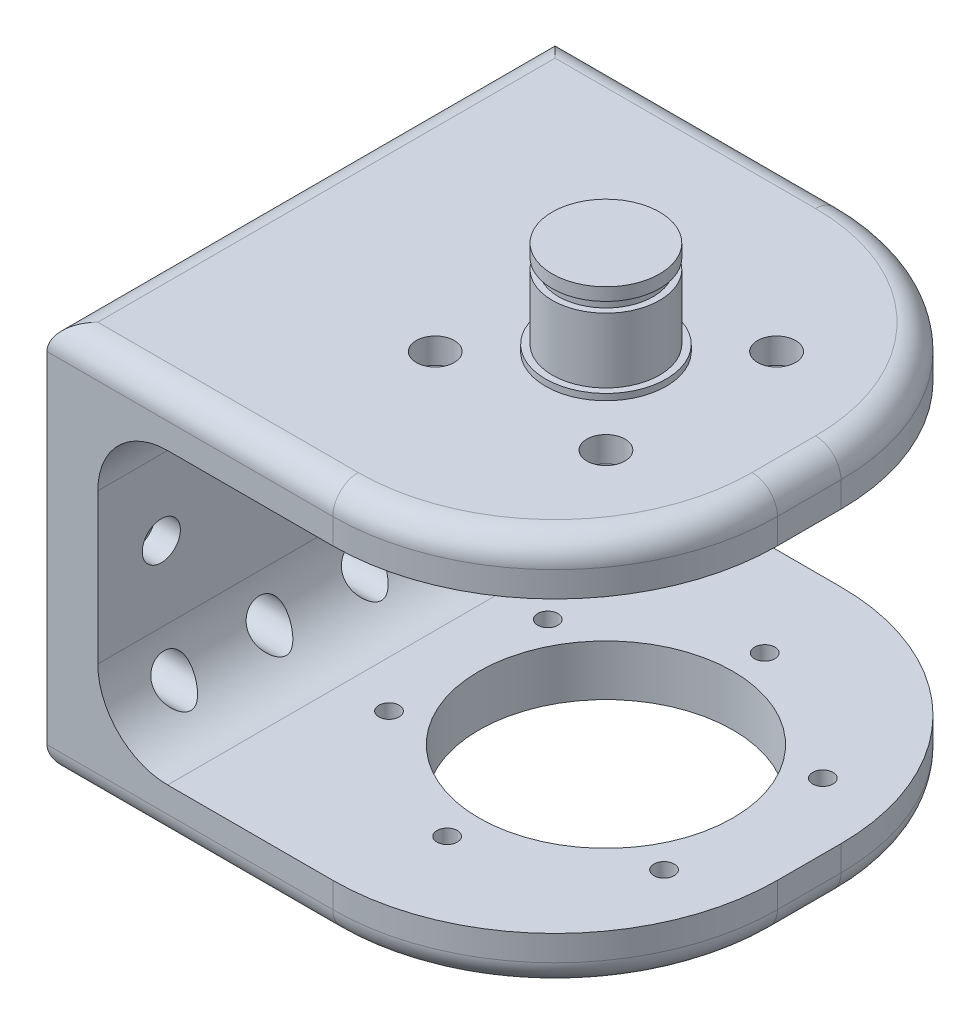
SolidWorks part; units mm, degrees
material "PETG-CF"
ref_plane "Front Plane" through (0, 0, 0) normal (0, 0, 1) x (1, 0, 0)
ref_plane "Top Plane" through (0, 0, 0) normal (0, 1, 0) x (1, 0, 0)
ref_plane "Right Plane" through (0, 0, 0) normal (1, 0, 0) x (0, 0, -1)
sketch "草图1" plane through (0, 0, 0) normal (0, 1, 0) x (1, 0, 0)
  line L1 (40, -40) -> (-40, -40)
  line L2 (40, -40) -> (40, 40)
  line L3 (40, 40) -> (-40, 40)
  line L4 (-40, -40) -> (-40, 40)
  line L5 (40, -40) -> (-40, 40) construction
  line L6 (40, 40) -> (-40, -40) construction
  point P0 (0, 0)
  dimension "D1" = 80
  dimension "D2" = 80
extrude "凸台-拉伸1" add sketch "草图1" along normal blind 8
sketch "草图2" plane through (0, 8, 0) normal (0, 1, 0) x (1, 0, 0)
  line L0 (-40, -40) -> (40, -40) construction
  line L1 (-32, -40) -> (-40, -40)
  line L2 (-32, -40) -> (-32, 40)
  line L3 (-32, 40) -> (-40, 40)
  line L4 (-40, -40) -> (-40, 40)
  line L5 (-32, -40) -> (-40, 40) construction
  line L6 (-32, 40) -> (-40, -40) construction
  point P0 (-36, 0)
  dimension "D1" = 8
extrude "凸台-拉伸2" add sketch "草图2" along normal blind 53.6
sketch "草图5" plane through (-32, 0, 0) normal (1, 0, 0) x (0, 0, -1)
  line L0 (-40, 61.6) -> (-40, 8) construction
  line L1 (40, 53.6) -> (-40, 53.6)
  line L2 (40, 53.6) -> (40, 61.6)
  line L3 (40, 61.6) -> (-40, 61.6)
  line L4 (-40, 53.6) -> (-40, 61.6)
  line L5 (40, 53.6) -> (-40, 61.6) construction
  line L6 (40, 61.6) -> (-40, 53.6) construction
  line L7 (40, 61.6) -> (40, 8) construction
  line L9 (-40, 61.6) -> (40, 61.6) construction
  point P0 (0, 57.6)
  dimension "D1" = 8
extrude "凸台-拉伸3" add sketch "草图5" along normal through all
sketch "草图4" plane through (0, 8, 0) normal (0, 1, 0) x (1, 0, 0)
  line L0 (-40, 40) -> (-40, -40) construction
  line L2 (40, -40) -> (40, 40) construction
  circle A0 centre (8, 0) radius 25 construction
  circle A1 centre (8, 25) radius 1.6
  circle A2 centre (-13.6506, 12.5) radius 1.6
  circle A3 centre (-13.6506, -12.5) radius 1.6
  circle A4 centre (8, -25) radius 1.6
  circle A5 centre (8, 0) radius 20
  circle A6 centre (29.6506, -12.5) radius 1.6
  circle A7 centre (29.6506, 12.5) radius 1.6
  point P17 (8, 0)
  point P22 (-40, 0)
  dimension "D3" = 50
  dimension "D4" = 3.2
  dimension "D6" = 40
  dimension "D1" = 32
  dimension "D5" = 6
extrude "切除-拉伸1" cut sketch "草图4" against normal through all contours A5 | A2 | A1 | A4 | A3 | A7 | A6
sketch "草图7" plane through (0, 61.6, 0) normal (0, 1, 0) x (1, 0, 0)
  line L0 (40, 40) -> (40, -40) construction
  line L3 (8, 0) -> (-5.435, 13.435) construction
  line L4 (8, 0) -> (8, 19) construction
  circle A0 centre (8, 0) radius 19 construction
  circle A5 centre (-5.435, 13.435) radius 1.6
  circle A6 centre (21.435, 13.435) radius 1.6
  circle A7 centre (21.435, -13.435) radius 1.6
  circle A8 centre (-5.435, -13.435) radius 1.6
  point P10 (40, 0)
  point P20 (8, 0)
  dimension "D1" = 38
  dimension "D4" = 45
  dimension "D5" = 3.2
  dimension "D6" = 4
extrude "切除-拉伸3" cut sketch "草图7" against normal up to next
fillet "圆角3" radius 35 4 edges at (40, 4, 40) (40, 4, -40) (40, 57.6, -40) (40, 57.6, 40)
fillet "圆角4" radius 11 2 edges at (-32, 8, 0) (-32, 53.6, 0)
sketch "草图6" plane through (-40, 0, 0) normal (-1, 0, 0) x (0, 0, 1)
  line L1 (30, 13) -> (-30, 13) construction
  line L2 (30, 13) -> (30, 48.6) construction
  line L3 (30, 48.6) -> (-30, 48.6) construction
  line L4 (-30, 13) -> (-30, 48.6) construction
  line L5 (30, 13) -> (-30, 48.6) construction
  line L6 (30, 48.6) -> (-30, 13) construction
  line L8 (40, 61.6) -> (40, 0) construction
  line L9 (-40, 61.6) -> (-40, 0) construction
  line L10 (-30, 30.8) -> (30, 30.8) construction
  line L11 (0, 13) -> (0, 48.6) construction
  line L12 (-40, 61.6) -> (40, 61.6) construction
  line L13 (-40, 0) -> (40, 0) construction
  circle A0 centre (-30, 48.6) radius 1.6
  circle A1 centre (30, 48.6) radius 1.6
  circle A2 centre (30, 13) radius 1.6
  circle A3 centre (-30, 13) radius 1.6
  circle A4 centre (-15, 13) radius 1.6
  circle A5 centre (0, 13) radius 1.6
  circle A6 centre (15, 13) radius 1.6
  circle A7 centre (-30, 30.8) radius 1.6
  circle A8 centre (30, 30.8) radius 1.6
  point P0 (0, 30.8)
  dimension "D5" = 3.2
  dimension "D1" = 13
  dimension "D2" = 13
  dimension "D3" = 10
  dimension "D4" = 10
  dimension "D6" = 4
  dimension "D7" = 2
extrude "切除-拉伸2" cut sketch "草图6" against normal through all
sketch "草图8" plane through (0, 61.6, 0) normal (0, 1, 0) x (1, 0, 0)
  circle A0 centre (8, 0) radius 8.45
  dimension "D1" = 16.9
extrude "凸台-拉伸4" add sketch "草图8" along normal blind 14.8
ref_plane "基准面1" through (0, 74.4, 0) normal (0, 1, 0) x (1, 0, 0)
sketch "草图10" plane through (0, 74.4, 0) normal (0, 1, 0) x (1, 0, 0)
  circle A0 centre (8, 0) radius 8.45
  circle A1 centre (8, 0) radius 7.45
  dimension "D1" = 14.9
extrude "切除-拉伸4" cut sketch "草图10" against normal blind 1.6
ref_plane "基准面2" through (-36, 0, 0) normal (-1, 0, 0) x (0, 0, 1)
sketch "草图12" plane through (-36, 0, 0) normal (-1, 0, 0) x (0, 0, 1)
  line L0 (-40, 30.8) -> (40, 30.8) construction
  line L1 (-40, 61.6) -> (-40, 0) construction
  line L2 (40, 61.6) -> (40, 0) construction
  line L3 (0, 61.6) -> (0, 0) construction
  line L4 (8.45, 61.6) -> (-8.45, 61.6) construction
  line L5 (-30, 13) -> (-30, 30.8) construction
  circle A0 centre (-30, 48.6) radius 3
  circle A1 centre (30, 48.6) radius 3
  circle A2 centre (30, 13) radius 3
  circle A3 centre (-30, 13) radius 3
  circle A4 centre (-15, 13) radius 3
  circle A5 centre (0, 13) radius 3
  circle A6 centre (15, 13) radius 3
  circle A7 centre (-30, 30.8) radius 3
  circle A8 centre (30, 30.8) radius 3
  dimension "D1" = 6
  dimension "D4" = 17.8
  dimension "D2" = 4
  dimension "D3" = 2
extrude "切除-拉伸5" cut sketch "草图12" against normal up to next
sketch "草图14" plane through (0, 61.6, 0) normal (0, 1, 0) x (1, 0, 0)
  circle A0 centre (-5.435, 13.435) radius 3
  circle A1 centre (21.435, 13.435) radius 3
  circle A2 centre (21.435, -13.435) radius 3
  circle A3 centre (-5.435, -13.435) radius 3
  point P12 (8, 0)
  dimension "D1" = 6
  dimension "D2" = 4
extrude "切除-拉伸6" cut sketch "草图14" against normal blind 4
sketch "草图15" plane through (0, 0, 0) normal (0, -1, 0) x (1, 0, 0)
  circle A0 centre (-13.6506, 12.5) radius 3
  circle A1 centre (8, 25) radius 3
  circle A2 centre (29.6506, 12.5) radius 3
  circle A3 centre (29.6506, -12.5) radius 3
  circle A4 centre (8, -25) radius 3
  circle A5 centre (-13.6506, -12.5) radius 3
  point P15 (8, 0)
  dimension "D1" = 6
  dimension "D2" = 6
extrude "切除-拉伸7" cut sketch "草图15" against normal blind 4
sketch "草图16" plane through (0, 61.6, 0) normal (0, 1, 0) x (1, 0, 0)
  circle A0 centre (8, 0) radius 9.5
  dimension "D1" = 19
extrude "凸台-拉伸5" add sketch "草图16" along normal blind 1
fillet "Fillet2" radius 4 12 edges at (-17.5, 0, -40) (29.7487, 0, -29.7487) (40, 0, 0) (29.7487, 0, 29.7487) (-17.5, 61.6, 40) (-17.5, 61.6, -40) (29.7487, 61.6, -29.7487) (40, 61.6, 0) (-40, 61.6, 0) (-40, 0, 0) (-17.5, 0, 40) (29.7487, 61.6, 29.7487)
